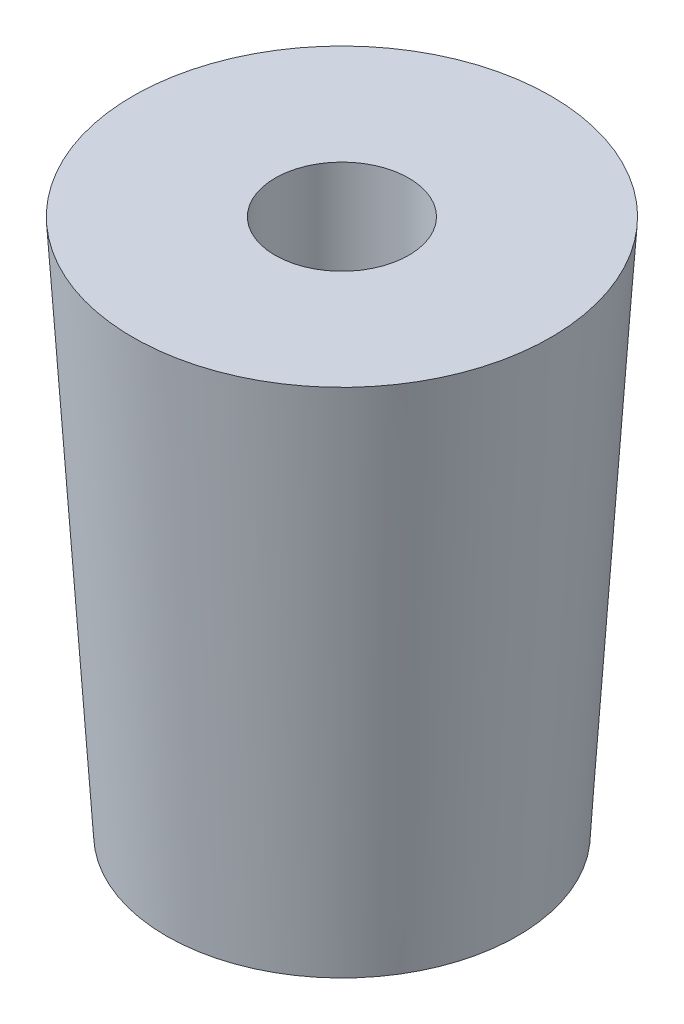
SolidWorks part; units mm, degrees
ref_plane "Front Plane" through (0, 0, 0) normal (0, 0, 1) x (1, 0, 0)
ref_plane "Top Plane" through (0, 0, 0) normal (0, 1, 0) x (1, 0, 0)
ref_plane "Right Plane" through (0, 0, 0) normal (1, 0, 0) x (0, 0, -1)
sketch "Sketch2" plane through (0, 0, 0) normal (1, 0, 0) x (0, 0, -1)
  line L0 (0, 0) -> (0, 25.4) construction
  line L1 (0, 0) -> (8.3344, 0)
  line L2 (8.3344, 0) -> (9.9219, 25.4)
  line L3 (9.9219, 25.4) -> (0, 25.4)
  line L4 (0, 0) -> (0, 25.4)
  dimension "D1" = 25.4
  dimension "D2" = 8.3344
  dimension "D3" = 9.9219
revolve "Revolve1" add sketch "Sketch2" angle 360 about L0
sketch "Sketch3" plane through (0, 25.4, 0) normal (0, 1, 0) x (1, 0, 0)
  circle A0 centre (0, 0) radius 3.175
  circle A1 centre (0, 0) radius 9.9219 construction
  dimension "D1" = 6.35
extrude "Cut-Extrude1" cut sketch "Sketch3" against normal through all
